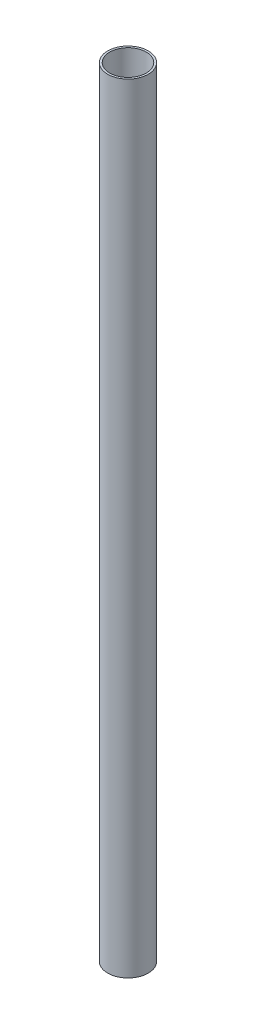
SolidWorks part; units mm, degrees
material "Thornel Mat VMA"
ref_plane "Front Plane" through (0, 0, 0) normal (0, 0, 1) x (1, 0, 0)
ref_plane "Top Plane" through (0, 0, 0) normal (0, 1, 0) x (1, 0, 0)
ref_plane "Right Plane" through (0, 0, 0) normal (1, 0, 0) x (0, 0, -1)
sketch "Sketch1" plane through (0, 0, 0) normal (0, 1, 0) x (1, 0, 0)
  circle A0 centre (0, 0) radius 15.875
  circle A1 centre (0, 0) radius 14.2875
  dimension "D1" = 31.75
  dimension "D2" = 1.5875
extrude "Boss-Extrude1" add sketch "Sketch1" along normal mid plane 609.6
